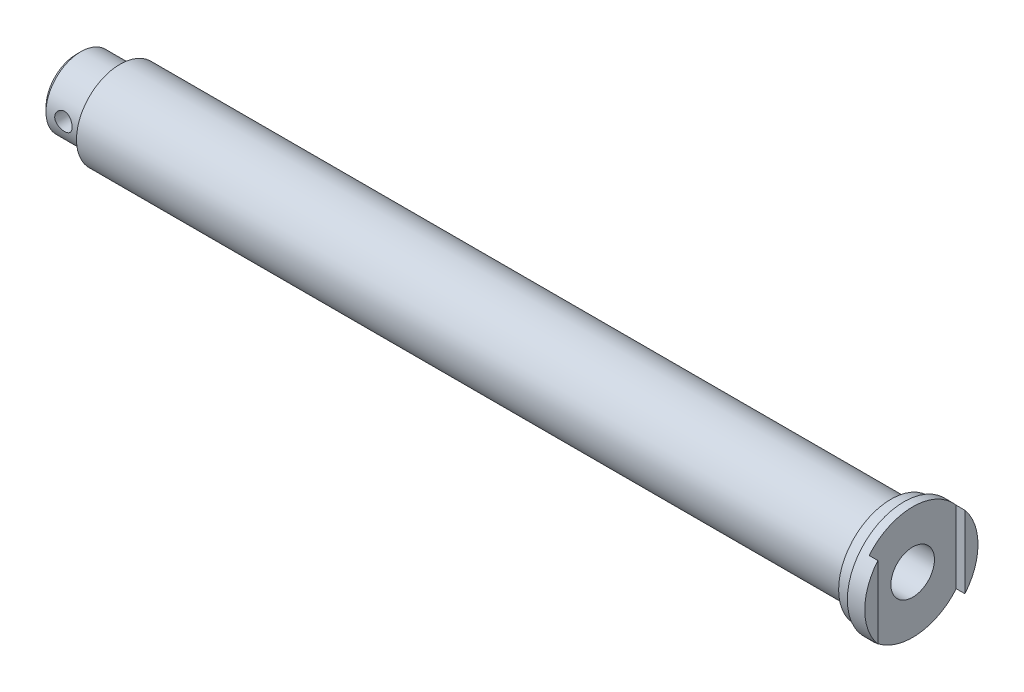
SolidWorks part; units mm, degrees
material "5052-H32"
ref_plane "Front Plane" through (0, 0, 0) normal (0, 0, 1) x (1, 0, 0)
ref_plane "Top Plane" through (0, 0, 0) normal (0, 1, 0) x (1, 0, 0)
ref_plane "Right Plane" through (0, 0, 0) normal (1, 0, 0) x (0, 0, -1)
sketch "Sketch1" plane through (0, 0, 0) normal (0, 0, 1) x (1, 0, 0)
  line L0 (0, 0) -> (55.7113, 0) construction
  line L2 (-97, 0) -> (-97, 4)
  line L3 (-3.5, 5) -> (-3.5, 6)
  line L4 (-2, 6.5) -> (0, 6.5)
  line L5 (-92, -4) -> (-97, -4) construction
  line L6 (0, 0) -> (0, 6.5)
  line L7 (-24.5, 5) -> (-24.5, 6.5) construction
  line L8 (0, 0) -> (-97, 0)
  line L9 (-94.5, 4) -> (-94.5, 0) construction
  line L10 (-92, -5) -> (-3.5, -5) construction
  line L12 (-23.5, 5) -> (-23.5, 6.5) construction
  line L13 (-3.5, 6) -> (-2, 6)
  line L14 (-2, 6) -> (-2, 6.5)
  line L15 (-2, -6.5) -> (0, -6.5) construction
  line L16 (-3.5, -6) -> (-2, -6) construction
  line L17 (-92, 5) -> (-92, 4)
  line L18 (-92, 4) -> (-97, 4)
  line L19 (-92, 5) -> (-3.5, 5)
  dimension "D1" = 5
  dimension "D2" = 72.5
  dimension "D3" = 12
  dimension "D4" = 20
  dimension "D5" = 10
  dimension "D6" = 1
  dimension "D7" = 13
  dimension "D8" = 1.5
  dimension "D9" = 2
  dimension "D10" = 8
revolve "Revolve1" add sketch "Sketch1" angle 360 about L0
sketch "Sketch4" plane through (0, 0, 0) normal (1, 0, 0) x (0, 0, -1)
  line L1 (-5, -6.5) -> (5, -6.5)
  line L2 (-5, -6.5) -> (-5, 6.5)
  line L3 (-5, 6.5) -> (5, 6.5)
  line L4 (5, -6.5) -> (5, 6.5)
  line L5 (-5, -6.5) -> (5, 6.5) construction
  line L6 (-5, 6.5) -> (5, -6.5) construction
  circle A0 centre (0, 0) radius 6.5 construction
  point P0 (0, 0)
  dimension "D1" = 10
extrude "Cut-Extrude2" cut sketch "Sketch4" against normal blind 1
hole_wizard "M6 Tapped Hole1" positions "Sketch5" profile "Sketch7" tap size "M6" standard "ISO"
sketch "Sketch5" plane through (-1, 0, 0) normal (1, 0, 0) x (0, 0, -1)
  point P0 (0, 0)
sketch "Sketch7" plane through (-1, 0, 0) normal (0, 1, 0) x (0, 0, -1)
  line L0 (0, 0) -> (0, 11.5022)
  line L1 (0, 11.5022) -> (2.5, 10)
  line L2 (2.5, 10) -> (2.5, 0)
  line L5 (2.5, 0) -> (0, 0)
  line L10 (0, 11.5022) -> (-2.5, 10) construction
  line L11 (0, -6.35) -> (0, 107.95) construction
  dimension "Tap Drill Dia." = 5
  dimension "Tap Drill Depth" = 10
  dimension "Drill Angle" = 118
cosmetic thread "Hole Thread1" parameters "D1"=10, "D2"=6
sketch "Sketch8" plane through (0, 0, 0) normal (0, 0, 1) x (1, 0, 0)
  circle A0 centre (-94.5, 0) radius 1
  dimension "D1" = 2
extrude "Cut-Extrude3" cut sketch "Sketch8" against normal through all both and the other way through all
chamfer "Chamfer1" distance 0.5 angle 45 1 edges at (-97, 0, 4)
